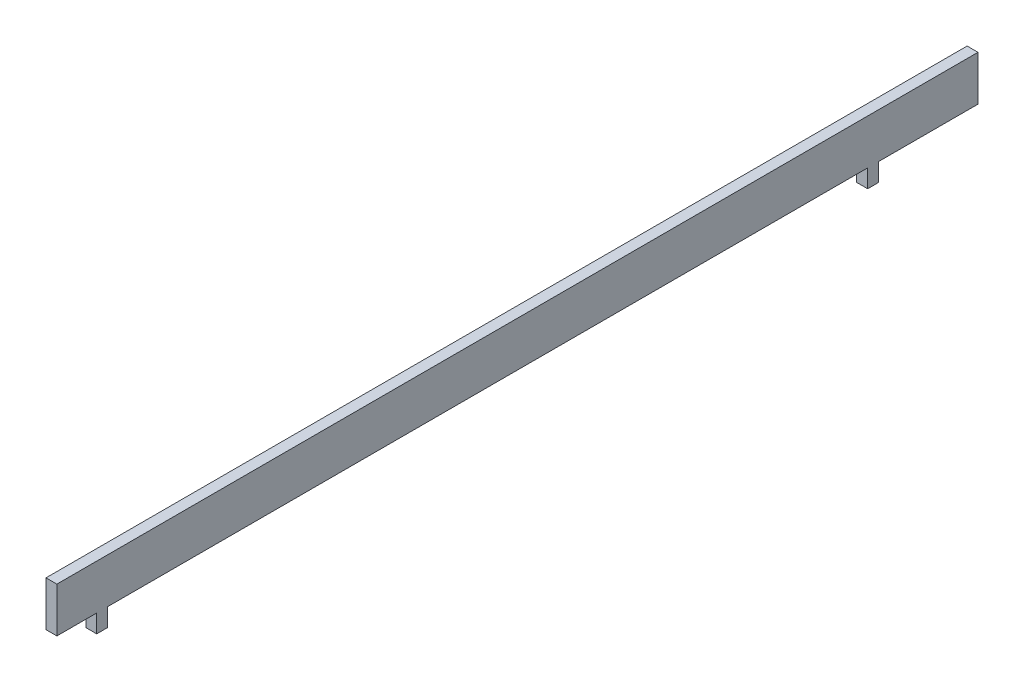
SolidWorks part; units mm, degrees
ref_plane "Front Plane" through (0, 0, 0) normal (0, 0, 1) x (1, 0, 0)
ref_plane "Top Plane" through (0, 0, 0) normal (0, 1, 0) x (1, 0, 0)
ref_plane "Right Plane" through (0, 0, 0) normal (1, 0, 0) x (0, 0, -1)
sketch "Sketch1" plane through (0, 0, 0) normal (1, 0, 0) x (0, 0, -1)
  line L0 (0, 0) -> (0, 57.5036) construction
  line L1 (320, 76) -> (574.5, 76)
  line L2 (320, 76) -> (320, 96)
  line L3 (320, 96) -> (574.5, 96)
  line L4 (574.5, 76) -> (574.5, 96)
  line L5 (0, 0) -> (23.1072, 0) construction
  dimension "D1" = 76
  dimension "D2" = 20
  dimension "D3" = 320
  dimension "D4" = 574.5
extrude "Boss-Extrude1" add sketch "Sketch1" along normal mid plane 3
sketch "Sketch2" plane through (0, 0, 0) normal (1, 0, 0) x (0, 0, -1)
  line L0 (0, 0) -> (693.6153, 0) construction
  line L1 (345, 115.5743) -> (345, 37.0202) construction
  line L2 (533, 118.1175) -> (533, 37.0202) construction
  line L3 (558, 120.8638) -> (558, 50.3348) construction
  line L4 (0, 0) -> (0, 58.2588) construction
  line L5 (320, 83.6) -> (331, 83.6)
  line L6 (331, 83.6) -> (331, 78.6)
  line L7 (331, 78.6) -> (334, 78.6)
  line L8 (334, 78.6) -> (334, 83.6)
  line L9 (544, 83.6) -> (544, 78.6)
  line L10 (547, 83.6) -> (547, 78.6)
  line L11 (320, 83.6) -> (320, 65.2358)
  line L12 (320, 65.2358) -> (574.5, 65.2358)
  line L13 (574.5, 65.2358) -> (574.5, 83.6)
  line L14 (544, 78.6) -> (547, 78.6)
  line L15 (533, 105.0606) -> (558, 105.0606) construction
  line L16 (320, 91.2373) -> (345, 91.2373) construction
  line L17 (545.5, 105.0606) -> (545.5, 100.804) construction
  line L18 (332.5, 91.2373) -> (332.5, 108.4876) construction
  line L19 (320, 96) -> (320, 76) construction
  line L20 (574.5, 76) -> (574.5, 96) construction
  line L21 (547, 83.6) -> (574.5, 83.6)
  line L22 (334, 83.6) -> (544, 83.6)
  point P26 (545.5, 105.0606)
  point P31 (332.5, 78.6)
  point P32 (545.5, 78.6)
  dimension "D1" = 345
  dimension "D2" = 533
  dimension "D3" = 558
  dimension "D4" = 78.6
  dimension "D5" = 3
  dimension "D6" = 3
  dimension "D7" = 5
revolve "Cut-Revolve1" cut sketch "Sketch2" angle 360 mid plane about L0
